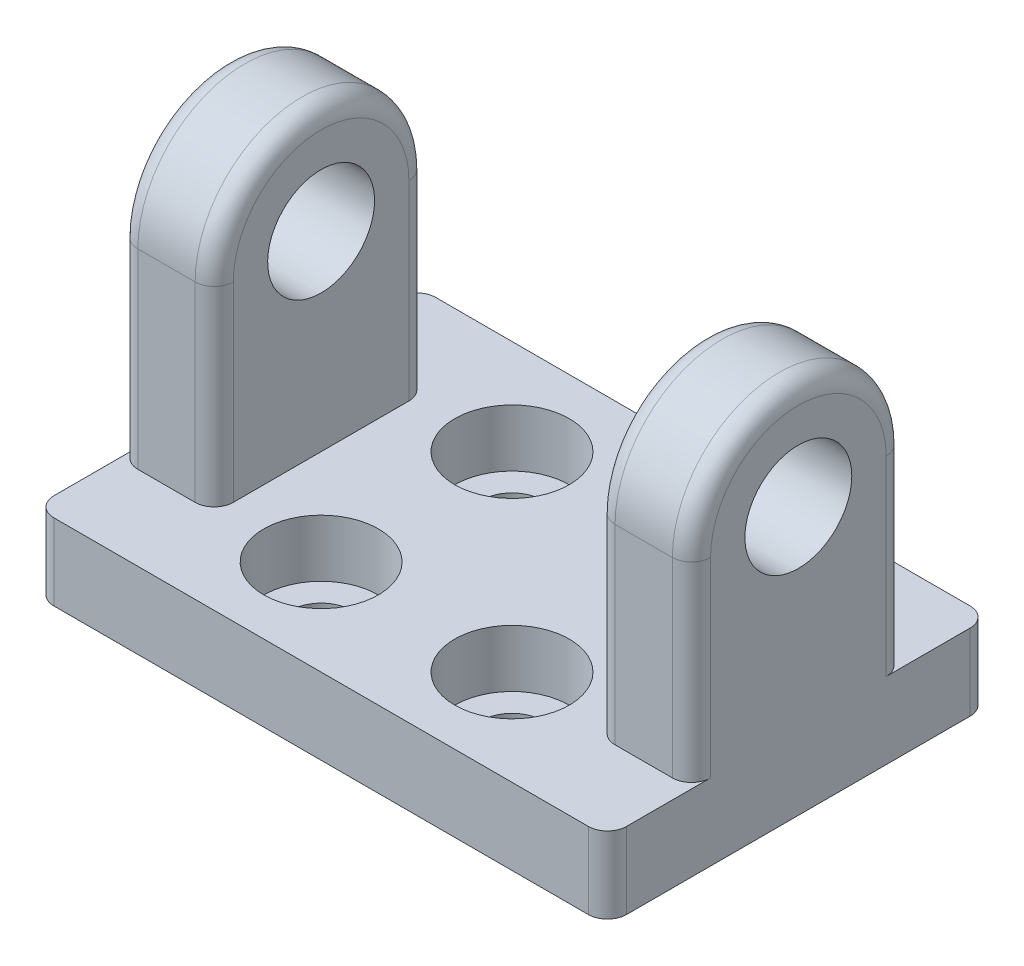
SolidWorks part; units mm, degrees
ref_plane "Plan de face" through (0, 0, 0) normal (0, 0, 1) x (1, 0, 0)
ref_plane "Plan de dessus" through (0, 0, 0) normal (0, 1, 0) x (1, 0, 0)
ref_plane "Plan de droite" through (0, 0, 0) normal (1, 0, 0) x (0, 0, -1)
sketch "Esquisse2" plane through (0, 0, 0) normal (1, 0, 0) x (0, 0, -1)
  line L0 (5.6, 0) -> (5.6, -10)
  line L2 (-5.6, 0) -> (-5.6, -10)
  line L3 (-5.6, -10) -> (5.6, -10)
  circle A0 centre (0, 0) radius 2.8
  arc A2 (5.6, 0) -> (-5.6, 0) centre (0, 0) ccw
  dimension "D1" = 5.6
  dimension "D2" = 10
  dimension "D3" = 5.6
  dimension "D4" = 5.6
extrude "Boss.-Extru.1" add sketch "Esquisse2" along normal mid plane 30
sketch "Esquisse4" plane through (0, -10, 0) normal (0, -1, 0) x (1, 0, 0)
  line L0 (-15, 5.6) -> (-15, -5.6) construction
  line L1 (-15, -10) -> (15, -10)
  line L2 (-15, -10) -> (-15, 10)
  line L3 (-15, 10) -> (15, 10)
  line L4 (15, -10) -> (15, 10)
  line L5 (15, 5.6) -> (15, -5.6) construction
  dimension "D1" = 20
  dimension "D4" = 10
extrude "Boss.-Extru.2" add sketch "Esquisse4" along normal blind 4
sketch "Esquisse5" plane through (0, -10, 0) normal (0, 1, 0) x (1, 0, 0)
  circle A0 centre (5, -5) radius 1.6
  circle A1 centre (5, 5) radius 1.6
  circle A2 centre (-5, 5) radius 1.6
  circle A3 centre (-5, -5) radius 1.6
  point P15 (0, 0)
  dimension "D1" = 3.2
  dimension "D2" = 10
  dimension "D3" = 10
  dimension "D4" = 5
  dimension "D5" = 5
extrude "Enlèv. mat.-Extru.1" cut sketch "Esquisse5" against normal up to next contours A0
sketch "Esquisse6" plane through (0, 0, 5.6) normal (0, 0, 1) x (1, 0, 0)
  line L0 (15, -10) -> (6.4832, -10) construction
  line L1 (-10, 11.5437) -> (10, 11.5437)
  line L2 (-10, 11.5437) -> (-10, -10)
  line L3 (-10, -10) -> (10, -10)
  line L4 (10, 11.5437) -> (10, -10)
  line L5 (15, 0) -> (-15, 0) construction
  point P7 (0, 11.5437)
  point P11 (0, 0)
  dimension "D2" = 20
extrude "Enlèv. mat.-Extru.2" cut sketch "Esquisse6" against normal through all
sketch "Esquisse7" plane through (0, -10, 0) normal (0, 1, 0) x (1, 0, 0)
  circle A4 centre (-5, 5) radius 3
  circle A5 centre (5, 5) radius 3
  circle A6 centre (5, -5) radius 3
  circle A7 centre (-5, -5) radius 3
  dimension "D1" = 6
extrude "Enlèv. mat.-Extru.3" cut sketch "Esquisse7" against normal blind 3
fillet "Congé1" radius 1 16 edges at (10, -5, -5.6) (10, -5, 5.6) (-10, -5, 5.6) (-10, -5, -5.6) (15, -5, -5.6) (15, -5, 5.6) (-15, -5, -5.6) (-15, -5, 5.6) (10, 5.6, 0) (-10, 5.6, 0) (15, 5.6, 0) (-15, 5.6, 0) (-15, -12, -10) (-15, -12, 10) (15, -12, -10) (15, -12, 10)
